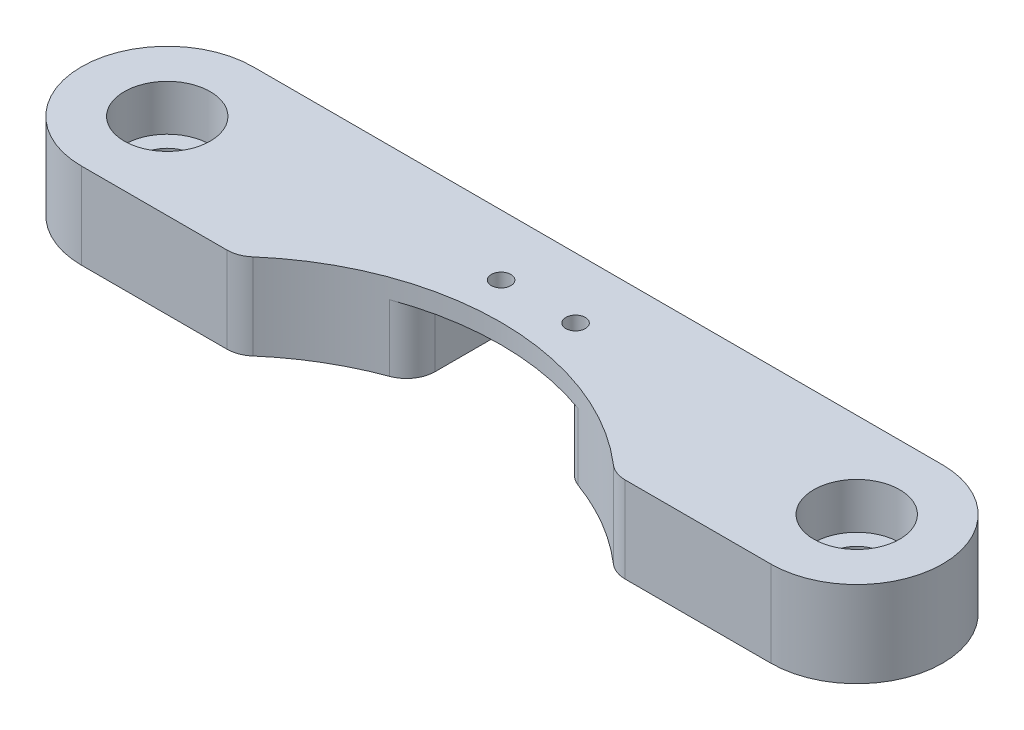
SolidWorks part; units mm, degrees
ref_plane "Front Plane" through (0, 0, 0) normal (0, 0, 1) x (1, 0, 0)
ref_plane "Top Plane" through (0, 0, 0) normal (0, 1, 0) x (1, 0, 0)
ref_plane "Right Plane" through (0, 0, 0) normal (1, 0, 0) x (0, 0, -1)
sketch "Sketch1" plane through (0, 45, 0) normal (0, 1, 0) x (1, 0, 0)
  line L0 (-16.5241, 17.5) -> (-30.2, 17.5)
  line L5 (-30.2, 32.5) -> (30, 32.5)
  line L7 (30, 17.5) -> (16.3241, 17.5)
  line L8 (-16.5241, 17.5) -> (16.3241, 17.5) construction
  circle A0 centre (-30.2, 25) radius 2.25
  circle A1 centre (30, 25) radius 2.25
  arc A2 (22.8385, 7.0588) -> (-23.0385, 7.0588) centre (-0.1, 0) ccw construction
  arc A3 (16.3241, 17.5) -> (-16.5241, 17.5) centre (-0.1, 0) ccw
  arc A6 (-30.2, 32.5) -> (-30.2, 17.5) centre (-30.2, 25) ccw
  arc A8 (30, 17.5) -> (30, 32.5) centre (30, 25) ccw
  dimension "D1" = 4.5
  dimension "D2" = 7.5
  dimension "D3" = 15
extrude "Boss-Extrude1" add sketch "Sketch1" along normal blind 7.5
sketch "Sketch2" plane through (0, 45, 0) normal (0, -1, 0) x (1, 0, 0)
  line L1 (-3.25, -21.9) -> (3.25, -21.9) construction
  line L2 (-3.25, -21.9) -> (-3.25, -27.2) construction
  line L3 (-3.25, -27.2) -> (3.25, -27.2) construction
  line L4 (3.25, -21.9) -> (3.25, -27.2) construction
  circle A0 centre (0, 0) radius 21.9 construction
  circle A1 centre (-3.25, -27.2) radius 0.85
  circle A2 centre (3.25, -27.2) radius 0.85
  point P9 (0, -21.9)
  dimension "D1" = 43.8
  dimension "D3" = 1.7
  dimension "D2" = 5.3
  dimension "D4" = 6.5
extrude "Cut-Extrude1" cut sketch "Sketch2" against normal through all
sketch "Sketch3" plane through (0, 52.5, 0) normal (0, -1, 0) x (1, 0, 0)
  line L0 (-3.25, -27.2) -> (3.25, -27.2) construction
  line L1 (-3.25, -24.7) -> (3.25, -24.7)
  line L2 (-3.25, -29.7) -> (3.25, -29.7)
  arc A0 (-3.25, -24.7) -> (-3.25, -29.7) centre (-3.25, -27.2) ccw
  arc A1 (3.25, -29.7) -> (3.25, -24.7) centre (3.25, -27.2) ccw
  circle A2 centre (3.25, -27.2) radius 0.85 construction
  circle A3 centre (-3.25, -27.2) radius 0.85 construction
  circle A4 centre (3.25, -27.2) radius 0.85
  circle A5 centre (-3.25, -27.2) radius 0.85
  point P4 (0, -27.2)
  dimension "D1" = 2.5
extrude "Boss-Extrude2" add sketch "Sketch3" along normal offset from surface (1.7 mm away) 5.8 up to face at (-3.25, 45, -28.05)
sketch "Sketch4" plane through (0, 45, 0) normal (0, 1, 0) x (1, 0, 0)
  line L0 (30, 32.5) -> (-30.2, 32.5) construction
  line L1 (-6.7, 23.0747) -> (6.5, 23.0747)
  line L2 (-6.7, 23.0747) -> (-6.7, 32.5)
  line L3 (-6.7, 32.5) -> (6.5, 32.5)
  line L4 (6.5, 23.0747) -> (6.5, 32.5)
  arc A0 (16.3241, 17.5) -> (-16.5241, 17.5) centre (-0.1, 0) ccw construction
  dimension "D1" = 13.2
extrude "Cut-Extrude2" cut sketch "Sketch4" along normal blind 5.8
fillet "Fillet1" radius 2.5 6 edges at (6.5, 47.9, -23.0747) (6.5, 47.9, -32.5) (-6.7, 47.9, -32.5) (-16.5241, 48.75, -17.5) (-6.7, 47.9, -23.0747) (16.3241, 48.75, -17.5)
sketch "Sketch5" plane through (0, 52.5, 0) normal (0, 1, 0) x (1, 0, 0)
  circle A0 centre (-30.2, 25) radius 3.75
  circle A1 centre (30, 25) radius 3.75
  dimension "D1" = 7.5
extrude "Cut-Extrude3" cut sketch "Sketch5" against normal blind 4
sketch "Sketch6" [suppressed] plane through (0, 52.5, 0) normal (0, 1, 0) x (1, 0, 0)
  line L1 (-26.65, 27.0496) -> (-30.2, 29.0992)
  line L2 (-30.2, 29.0992) -> (-33.75, 27.0496)
  line L3 (-33.75, 27.0496) -> (-33.75, 22.9504)
  line L4 (-33.75, 22.9504) -> (-30.2, 20.9008)
  line L5 (-30.2, 20.9008) -> (-26.65, 22.9504)
  line L6 (-26.65, 22.9504) -> (-26.65, 27.0496)
  line L7 (33.55, 27.0496) -> (30, 29.0992)
  line L8 (30, 29.0992) -> (26.45, 27.0496)
  line L9 (26.45, 27.0496) -> (26.45, 22.9504)
  line L10 (26.45, 22.9504) -> (30, 20.9008)
  line L11 (30, 20.9008) -> (33.55, 22.9504)
  line L12 (33.55, 22.9504) -> (33.55, 27.0496)
  circle A0 centre (-30.2, 25) radius 3.55 construction
  circle A1 centre (30, 25) radius 3.55 construction
  dimension "D1" = 7.1
extrude "Cut-Extrude4" [suppressed] cut sketch "Sketch6" against normal offset from surface (5.5 mm away) 2
